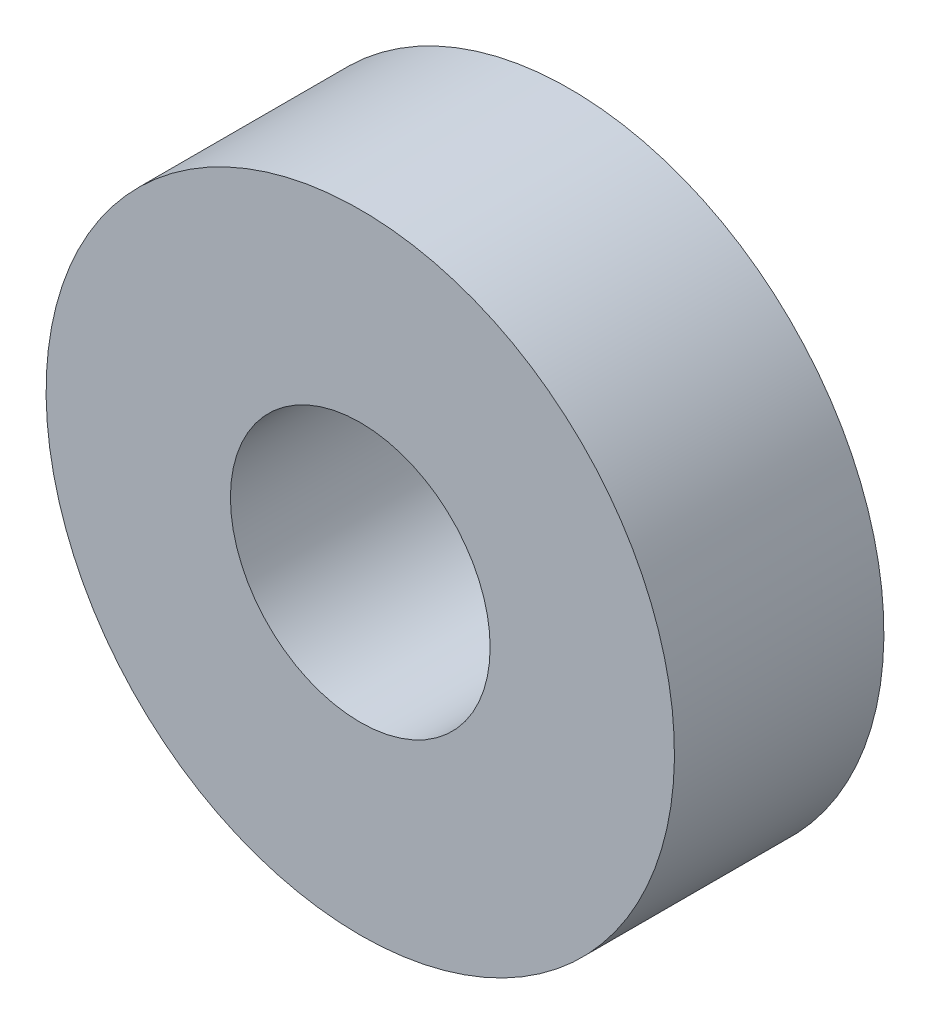
SolidWorks part; units mm, degrees
ref_plane "Front Plane" through (0, 0, 0) normal (0, 0, 1) x (1, 0, 0)
ref_plane "Top Plane" through (0, 0, 0) normal (0, 1, 0) x (1, 0, 0)
ref_plane "Right Plane" through (0, 0, 0) normal (1, 0, 0) x (0, 0, -1)
sketch "Sketch1" plane through (0, 0, 12.6) normal (0, 0, 1) x (1, 0, 0)
  circle A1 centre (-70, 14.1421) radius 3
  circle A2 centre (-70, 14.1421) radius 7.5
  arc A4 (-70.633, 21.6154) -> (-73.4637, 7.4898) centre (-70, 14.1421) ccw construction
  circle A5 centre (-70, 14.1421) radius 3 construction
extrude "Boss-Extrude1" add sketch "Sketch1" along normal up to surface (3.825 mm away)
sketch "Sketch2" plane through (0, 0, 12.6) normal (0, 0, -1) x (-1, 0, 0)
  circle A0 centre (70, 14.1421) radius 3 construction
  circle A1 centre (70, 14.1421) radius 7.5
  circle A2 centre (70, 14.1421) radius 7.5
  circle A3 centre (70, 14.1421) radius 3
  dimension "D1" = 0
extrude "Boss-Extrude2" add sketch "Sketch2" along normal offset from surface (1.175 mm away) 5 up to face at (-70, 11.1421, 16.425)
sketch "Sketch3" plane through (0, 0, 11.425) normal (0, 0, -1) x (-1, 0, 0)
  circle A0 centre (70, 14.1421) radius 3.1
  dimension "D1" = 6.2
extrude "Cut-Extrude1" cut sketch "Sketch3" against normal up to next
